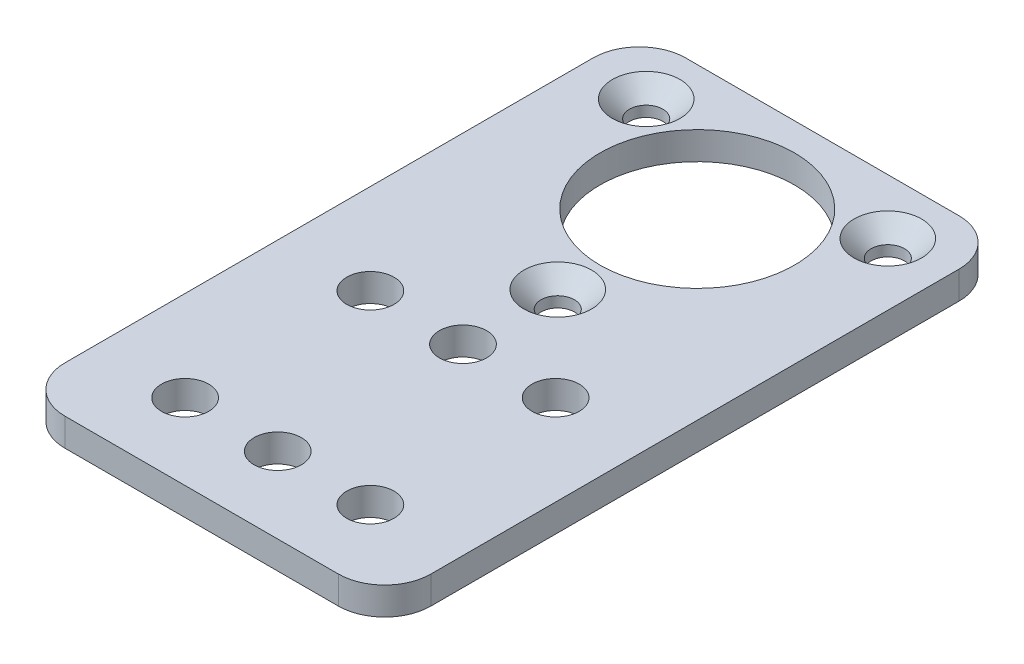
SolidWorks part; units mm, degrees
material "6061-T6 (SS)"
ref_plane "Front Plane" through (0, 0, 0) normal (0, 0, 1) x (1, 0, 0)
ref_plane "Top Plane" through (0, 0, 0) normal (0, 1, 0) x (1, 0, 0)
ref_plane "Right Plane" through (0, 0, 0) normal (1, 0, 0) x (0, 0, -1)
sketch "Sketch1" plane through (0, 0, 0) normal (0, 1, 0) x (1, 0, 0)
  line L0 (-19.75, 0) -> (0, 0) construction
  line L1 (14.75, -33.5) -> (-14.75, -33.5)
  line L2 (19.75, -28.5) -> (19.75, 28.5)
  line L3 (14.75, 33.5) -> (-14.75, 33.5)
  line L4 (-19.75, -28.5) -> (-19.75, 28.5)
  line L5 (0, 33.5) -> (0, 0) construction
  line L9 (10, -25.29) -> (0, -25.29) construction
  arc A0 (-14.75, -33.5) -> (-19.75, -28.5) centre (-14.75, -28.5) cw
  arc A1 (14.75, -33.5) -> (19.75, -28.5) centre (14.75, -28.5) ccw
  arc A2 (19.75, 28.5) -> (14.75, 33.5) centre (14.75, 28.5) ccw
  arc A3 (-14.75, 33.5) -> (-19.75, 28.5) centre (-14.75, 28.5) ccw
  circle A4 centre (0, 26.5) radius 2.55
  circle A7 centre (10, -25.29) radius 2.55
  circle A8 centre (10, -5.29) radius 2.55
  circle A9 centre (0, -25.29) radius 2.55
  circle A10 centre (0, -5.29) radius 2.55
  circle A11 centre (-10, -25.29) radius 2.55
  circle A12 centre (-10, -5.29) radius 2.55
  dimension "D2" = 5
  dimension "D3" = 7
  dimension "D7" = 20
  dimension "D10" = 3
  dimension "D8" = 9.75
  dimension "D6" = 5.1
  dimension "D1" = 67
  dimension "D9" = 39.5
  dimension "D11" = 10
  dimension "D12" = 8.21
extrude "Boss-Extrude1" add sketch "Sketch1" along normal blind 3
sketch "Sketch2" plane through (0, 3, 0) normal (0, 1, 0) x (1, 0, 0)
  line L0 (14.75, 33.5) -> (-14.75, 33.5) construction
  line L1 (-14.75, -33.5) -> (14.75, -33.5) construction
  circle A0 centre (0, 20) radius 19.75 construction
  circle A1 centre (0, 20) radius 10.5
  point P2 (0, 33.5)
  point P5 (0, -33.5)
  dimension "D1" = 0
  dimension "D2" = 53.5
extrude "Cut-Extrude2" cut sketch "Sketch2" against normal through all
sketch "Sketch3" plane through (0, 3, 0) normal (0, 1, 0) x (1, 0, 0)
  line L1 (0, 4.94) -> (13.0423, 27.53)
  line L2 (13.0423, 27.53) -> (-13.0423, 27.53)
  line L3 (-13.0423, 27.53) -> (0, 4.94)
  circle A0 centre (0, 20) radius 15.06
  circle A1 centre (0, 20) radius 15.06 construction
  circle A2 centre (13.0423, 27.53) radius 2.5
  circle A3 centre (-13.0423, 27.53) radius 2.5
  circle A4 centre (0, 4.94) radius 2.5
hole_wizard "CSK for M3 Flat Head Machine Screw1" positions "Sketch5" profile "Sketch4" countersink size "M3" standard "ANSI Metric" end condition through all
sketch "Sketch5" plane through (0, 3, 0) normal (0, 1, 0) x (1, 0, 0)
  point P0 (-13.0423, 27.53)
  point P3 (13.0423, 27.53)
  point P6 (0, 4.94)
sketch "Sketch4" plane through (-13.0423, 3, -27.53) normal (1, 0, 0) x (0, 0, 1)
  line L0 (0, 0) -> (0, 3)
  line L1 (0, 3) -> (1.8, 3)
  line L2 (1.8, 3) -> (1.8, 1.85)
  line L3 (1.8, 1.85) -> (3.65, 0)
  line L5 (3.65, 0) -> (0, 0)
  line L6 (-1.8, 1.85) -> (-3.65, 0) construction
  line L11 (0, -6.35) -> (0, 107.95) construction
  dimension "Thru Hole Dia." = 3.6
  dimension "Thru Hole Depth" = 3
  dimension "Near C'Sink Dia." = 7.3
  dimension "Near C'Sink Angle" = 90
